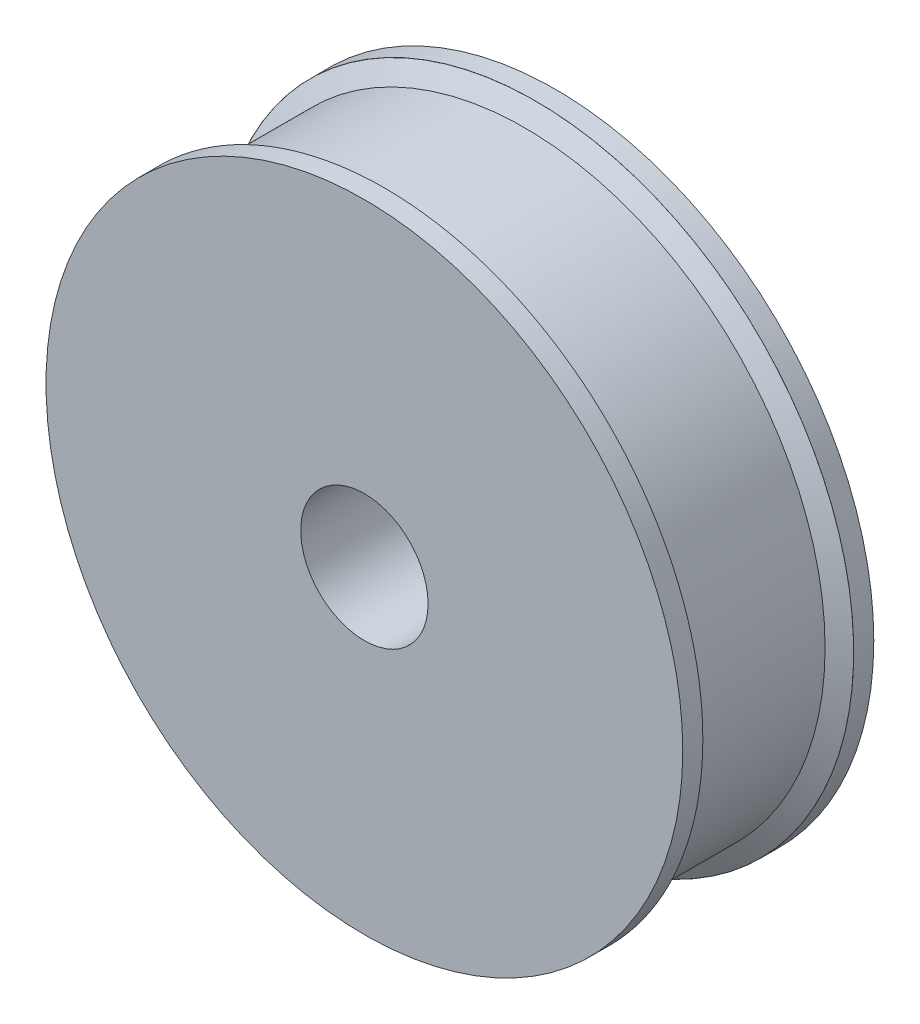
SolidWorks part; units mm, degrees
ref_plane "Alzado" through (0, 0, 0) normal (0, 0, 1) x (1, 0, 0)
ref_plane "Planta" through (0, 0, 0) normal (0, 1, 0) x (1, 0, 0)
ref_plane "Vista lateral" through (0, 0, 0) normal (1, 0, 0) x (0, 0, -1)
sketch "Croquis1" plane through (0, 0, 0) normal (0, 0, 1) x (1, 0, 0)
  circle A0 centre (0, 0) radius 31.75
  circle A1 centre (0, 0) radius 6.35
  dimension "D1" = 63.5
  dimension "D2" = 12.7
extrude "Saliente-Extruir1" add sketch "Croquis1" along normal blind 19.05
sketch "Croquis2" plane through (0, 0, 0) normal (1, 0, 0) x (0, 0, -1)
  line L1 (-3.0425, 29.935) -> (-16.0075, 29.935)
  line L2 (-16.0075, 29.935) -> (-17.05, 31.7407)
  line L3 (-2, 31.7407) -> (-3.0425, 29.935)
  line L4 (0, -31.75) -> (0, 31.75) construction
  line L5 (-19.05, 31.75) -> (-19.05, -31.75) construction
  line L6 (0, 0) -> (-19.05, 0) construction
  line L7 (-2, 31.7407) -> (-2, 32.935)
  line L8 (-2, 32.935) -> (-17.05, 32.935)
  line L9 (-17.05, 32.935) -> (-17.05, 31.7407)
  dimension "D1" = 2
  dimension "D2" = 2
  dimension "D3" = 3
  dimension "D4" = 60
  dimension "D5" = 60
revolve "Cortar-Revolución2" cut sketch "Croquis2" angle 360 about L6
